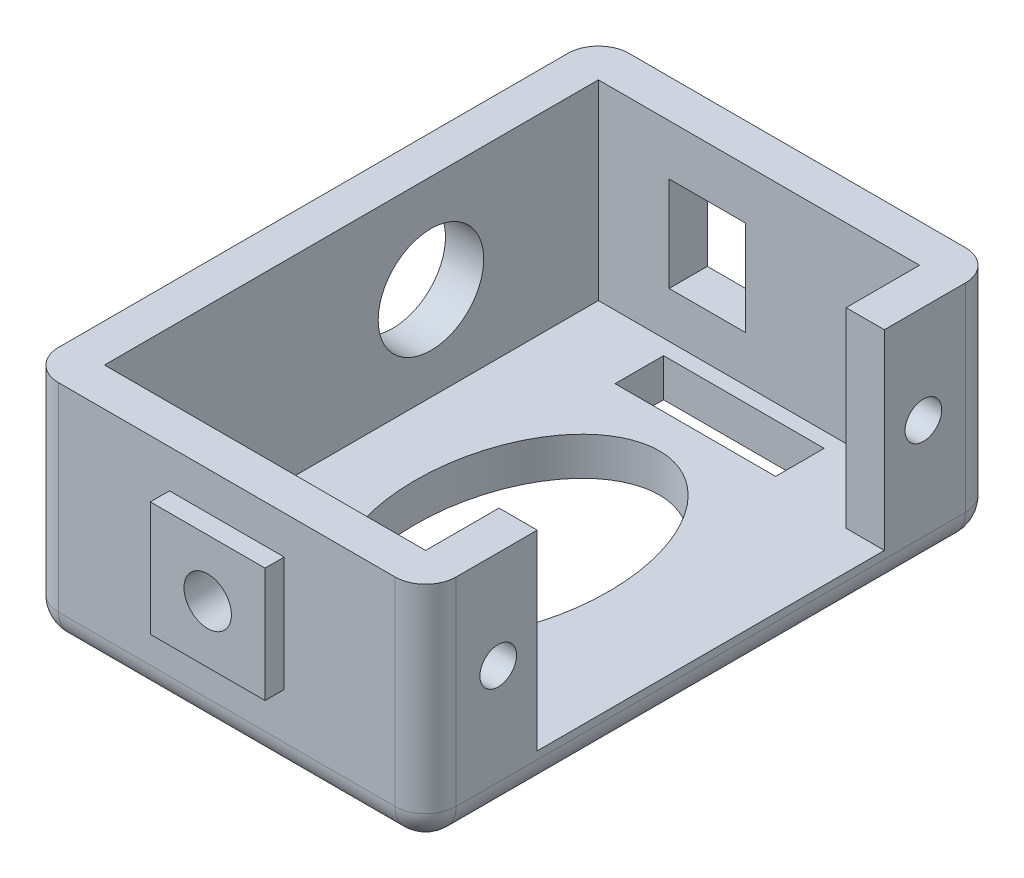
SolidWorks part; units mm, degrees
ref_plane "Front Plane" through (0, 0, 0) normal (0, 0, 1) x (1, 0, 0)
ref_plane "Top Plane" through (0, 0, 0) normal (0, 1, 0) x (1, 0, 0)
ref_plane "Right Plane" through (0, 0, 0) normal (1, 0, 0) x (0, 0, -1)
sketch "Sketch1" plane through (0, 0, 0) normal (0, 1, 0) x (1, 0, 0)
  line L1 (0, 29.9941) -> (-26, 29.9941)
  line L2 (-26, 29.9941) -> (-26, -7.3059)
  line L3 (-26, -7.3059) -> (0, -7.3059)
  line L4 (0, -7.3059) -> (0, -0.0059)
  line L5 (0, -0.0059) -> (-2.5, -0.0059)
  line L6 (-2.5, -0.0059) -> (-2.5, -4.8059)
  line L7 (-2.5, -4.8059) -> (-23.5, -4.8059)
  line L8 (-23.5, -4.8059) -> (-23.5, 27.4941)
  line L11 (0, 22.6941) -> (-2.5, 22.6941)
  line L13 (0, 29.9941) -> (0, 22.6941)
  line L14 (-23.5, 27.4941) -> (-2.5, 27.4941)
  line L15 (-2.5, 27.4941) -> (-2.5, 22.6941)
  dimension "D1" = 4.8
  dimension "D2" = 2.5
  dimension "D3" = 2.5
  dimension "D4" = 2.5
  dimension "D5" = 21
  dimension "D6" = 37.3
extrude "Boss-Extrude1" add sketch "Sketch1" along normal blind 15
sketch "Sketch2" plane through (-23.5, 0, 0) normal (1, 0, 0) x (0, 0, -1)
  line L5 (27.4941, 15) -> (27.4941, 0) construction
  line L6 (-4.8059, 0) -> (27.4941, 0)
  line L7 (-4.8059, 0) -> (-4.8059, 2.5)
  line L8 (-4.8059, 2.5) -> (27.4941, 2.5)
  line L9 (27.4941, 0) -> (27.4941, 2.5)
  dimension "D1" = 2.5
extrude "Boss-Extrude2" add sketch "Sketch2" along normal through all
sketch "Sketch3" plane through (0, 0, -29.9941) normal (0, 0, -1) x (-1, 0, 0)
  line L0 (26, 15) -> (26, 0) construction
  line L1 (13.875, 11.7) -> (18.875, 11.7)
  line L2 (13.875, 11.7) -> (13.875, 5.5)
  line L3 (13.875, 5.5) -> (18.875, 5.5)
  line L4 (18.875, 11.7) -> (18.875, 5.5)
  line L5 (0, 0) -> (26, 0) construction
  dimension "D1" = 6.2
  dimension "D2" = 5
  dimension "D3" = 7.125
  dimension "D4" = 5.5
extrude "Cut-Extrude1" cut sketch "Sketch3" against normal blind 12.5
sketch "Sketch4" plane through (-26, 0, 0) normal (-1, 0, 0) x (0, 0, 1)
  line L0 (-29.9941, 15) -> (7.3059, 15) construction
  line L1 (-29.9941, 15) -> (-29.9941, 0) construction
  circle A0 centre (-16.5441, 8.6) radius 3.45
  dimension "D1" = 6.9
  dimension "D2" = 6.4
  dimension "D3" = 13.45
extrude "Cut-Extrude2" cut sketch "Sketch4" against normal up to next
sketch "Sketch5" plane through (0, 0, 0) normal (1, 0, 0) x (0, 0, -1)
  line L0 (-0.0059, 15) -> (-0.0059, 2.5) construction
  line L1 (-7.3059, 15) -> (-0.0059, 15) construction
  circle A0 centre (-2.5559, 8.6) radius 1.2
  dimension "D2" = 2.4
  dimension "D1" = 2.55
  dimension "D3" = 6.4
extrude "Cut-Extrude3" cut sketch "Sketch5" against normal up to next (2.5 mm away)
ref_plane "Plane1" through (0, 0, -11.3441) normal (0, 0, 1) x (1, 0, 0)
mirror "Mirror1" about plane through (0, 0, -11.3441) normal (0, 0, 1) of "Cut-Extrude3"
sketch "Sketch6" plane through (0, 0, 7.3059) normal (0, 0, 1) x (1, 0, 0)
  line L0 (-2.5, 15) -> (-2.5, 2.5) construction
  line L1 (-23.5, 15) -> (-23.5, 2.5) construction
  line L2 (-2.5, 15) -> (-2.5, 2.5) construction
  line L3 (-23.5, 15) -> (-23.5, 2.5) construction
  line L4 (-23.5, 8.75) -> (-19, 8.75) construction
  line L5 (-19, 8.75) -> (-13, 8.75) construction
  line L6 (-13, 8.75) -> (-7, 8.75) construction
  line L7 (-7, 8.75) -> (-2.5, 8.75) construction
  circle A1 centre (-13, 8.75) radius 1.55
  dimension "D1" = 3.1
  dimension "D2" = 4.5
extrude "Cut-Extrude4" cut sketch "Sketch6" against normal up to next
fillet "Fillet2" radius 2 8 edges at (0, 0, -11.3441) (-13, 0, -29.9941) (-26, 0, -11.3441) (0, 7.5, -29.9941) (-26, 7.5, -29.9941) (0, 7.5, 7.3059) (-26, 7.5, 7.3059) (-13, 0, 7.3059)
sketch "Sketch7" plane through (0, 0, 7.3059) normal (0, 0, 1) x (1, 0, 0)
  line L1 (-16.75, 12.5) -> (-9.25, 12.5)
  line L2 (-16.75, 12.5) -> (-16.75, 5)
  line L3 (-16.75, 5) -> (-9.25, 5)
  line L4 (-9.25, 12.5) -> (-9.25, 5)
  circle A0 centre (-13, 8.75) radius 1.55 construction
  circle A1 centre (-13, 8.75) radius 1.55
  point P8 (-13, 12.5)
  point P10 (-9.25, 8.75)
  dimension "D1" = 7.5
sketch "Sketch8" plane through (0, 2.5, 0) normal (0, 1, 0) x (1, 0, 0)
  line L0 (-13, 1.7101) -> (-13, 11.3441) construction
  line L1 (-13, 11.3441) -> (-19.3129, 11.3441) construction
  line L2 (-13, -0.6439) -> (-13, 1.7101) construction
  line L3 (-7.75, -3.8189) -> (-18.25, -3.8189)
  line L4 (-2.5, -0.0059) -> (-13, -0.0059) construction
  line L5 (-13, -0.0059) -> (-23.5, -0.0059) construction
  line L6 (-23.5, 27.4941) -> (-23.5, -4.8059) construction
  line L7 (-7.75, -3.8189) -> (-7.75, -0.6439)
  line L8 (-7.75, -0.6439) -> (-18.25, -0.6439)
  line L9 (-18.25, -3.8189) -> (-18.25, -0.6439)
  line L10 (-7.75, 23.3321) -> (-18.25, 23.3321)
  line L11 (-7.75, 23.3321) -> (-7.75, 26.5071)
  line L12 (-7.75, 26.5071) -> (-18.25, 26.5071)
  line L13 (-18.25, 23.3321) -> (-18.25, 26.5071)
  line L14 (-13, 20.9781) -> (-13, 23.3321) construction
  line L15 (-13, 26.5071) -> (-13, 27.4941) construction
  line L16 (-2.5, 27.4941) -> (-23.5, 27.4941) construction
  line L17 (-1.375, 11.3441) -> (1.375, 11.3441) construction
  line L18 (-13, -3.8189) -> (-13, -4.8059) construction
  line L19 (-2.5, -4.8059) -> (-23.5, -4.8059) construction
  ellipse E3 centre (-13, 11.3441) end of major axis (-13, 20.9781) minor radius 6.3129
  point P15 (-13, 23.3321)
  point P16 (-13, -0.6439)
  dimension "D1" = 3.175
  dimension "D2" = 10.5
extrude "Cut-Extrude6" cut sketch "Sketch8" against normal up to next
extrude "Boss-Extrude3" add sketch "Sketch7" along normal blind 1.25
